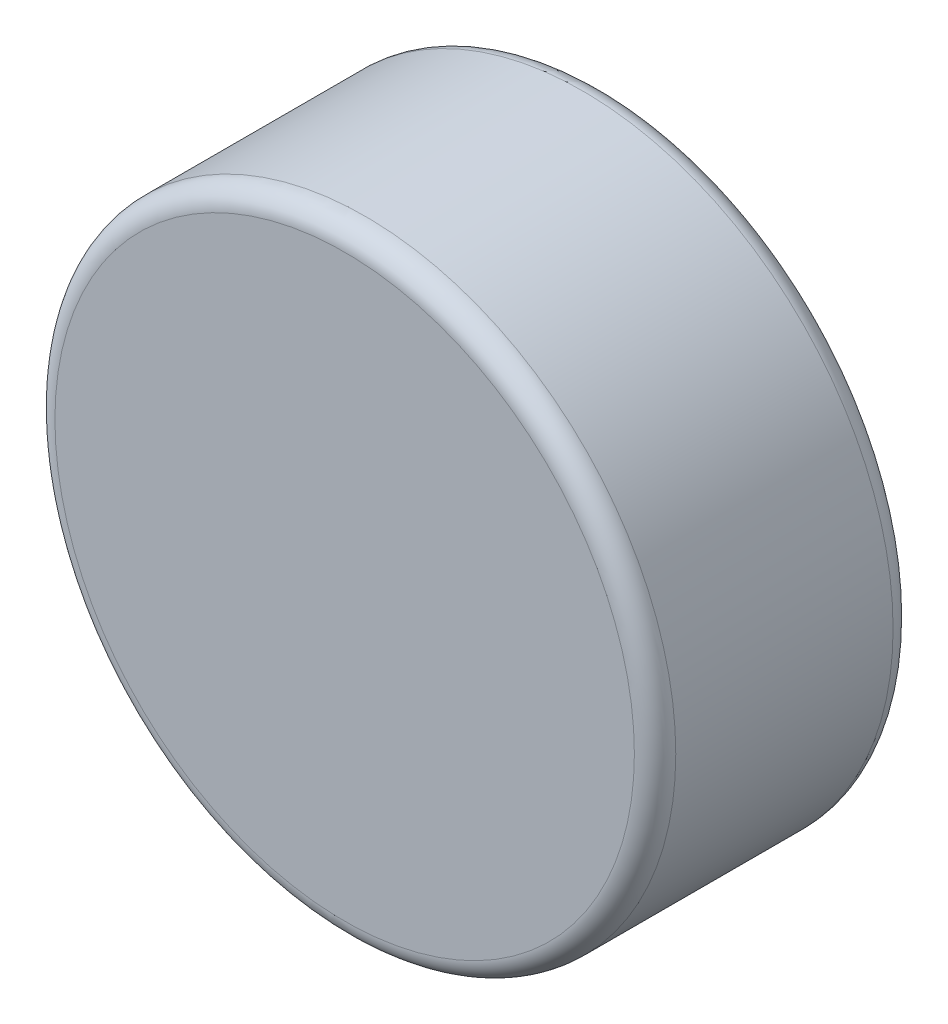
SolidWorks part; units mm, degrees
material "Nickel"
ref_plane "Front Plane" through (0, 0, 0) normal (0, 0, 1) x (1, 0, 0)
ref_plane "Top Plane" through (0, 0, 0) normal (0, 1, 0) x (1, 0, 0)
ref_plane "Right Plane" through (0, 0, 0) normal (1, 0, 0) x (0, 0, -1)
sketch "Sketch1" plane through (0, 0, 0) normal (0, 0, 1) x (1, 0, 0)
  circle A0 centre (0, 0) radius 3
  dimension "D1" = 6
extrude "Boss-Extrude1" add sketch "Sketch1" along normal blind 2.5
fillet "Fillet1" radius 0.2 2 edges at (3, 0, 0) (3, 0, 2.5)
